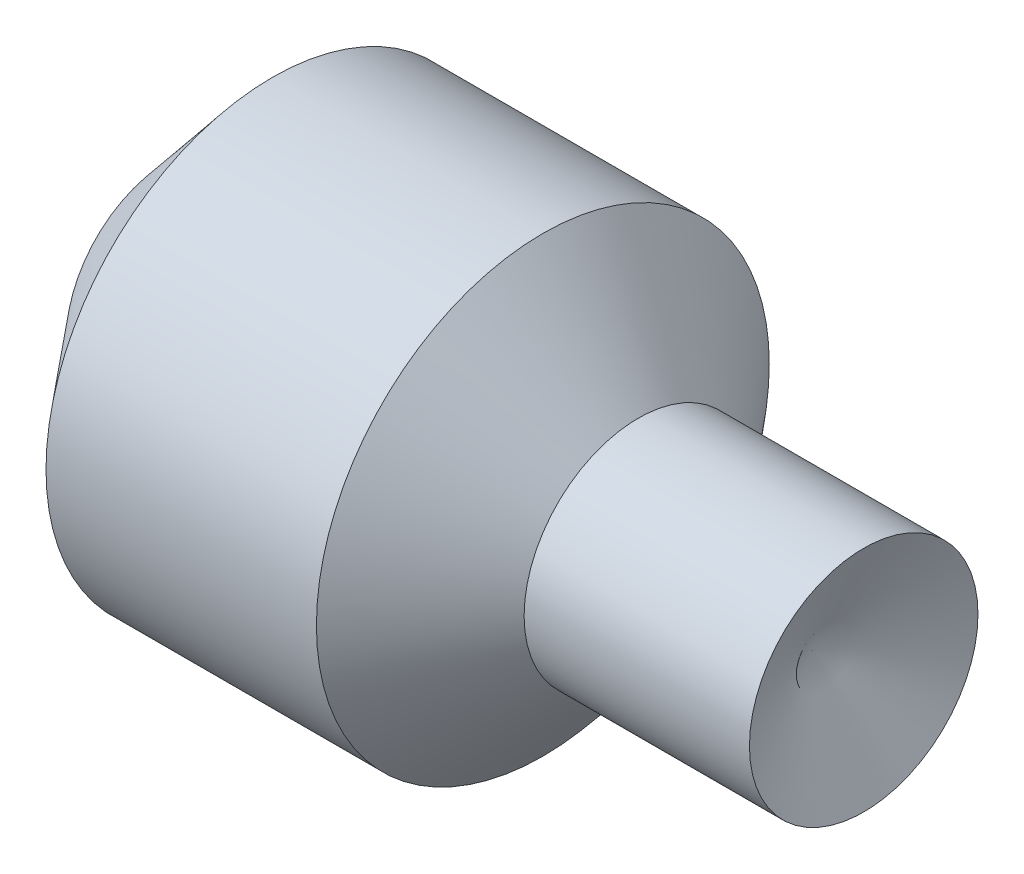
SolidWorks part; units mm, degrees
ref_plane "Alzado" through (0, 0, 0) normal (0, 0, 1) x (1, 0, 0)
ref_plane "Planta" through (0, 0, 0) normal (0, 1, 0) x (1, 0, 0)
ref_plane "Vista lateral" through (0, 0, 0) normal (1, 0, 0) x (0, 0, -1)
sketch "Croquis1" plane through (0, 0, 0) normal (0, 0, 1) x (1, 0, 0)
  line L1 (6.6327, 40.0045) -> (-43.0403, 40.0045)
  line L2 (-43.0403, 40.0045) -> (-64.1026, 64.7262)
  line L3 (-64.1026, 64.7262) -> (-96.2127, 64.7262)
  line L4 (-96.2127, 64.7262) -> (-123.7102, 64.7262)
  line L5 (-123.7102, 64.7262) -> (-146.2404, 37.7609)
  line L6 (-146.2404, 37.7609) -> (-156.6299, 14.8132)
  line L7 (-145.2246, 14.8132) -> (-4.7734, 14.8132)
  line L8 (-156.6299, 14.8132) -> (-145.2246, 14.8132)
  line L9 (6.6327, 40.0045) -> (-4.7734, 14.8132)
  dimension "D1" = 25.19
  dimension "D3" = 65.642
  dimension "D4" = 65.64
revolve "Revolución1" add sketch "Croquis1" angle 360 about L7
